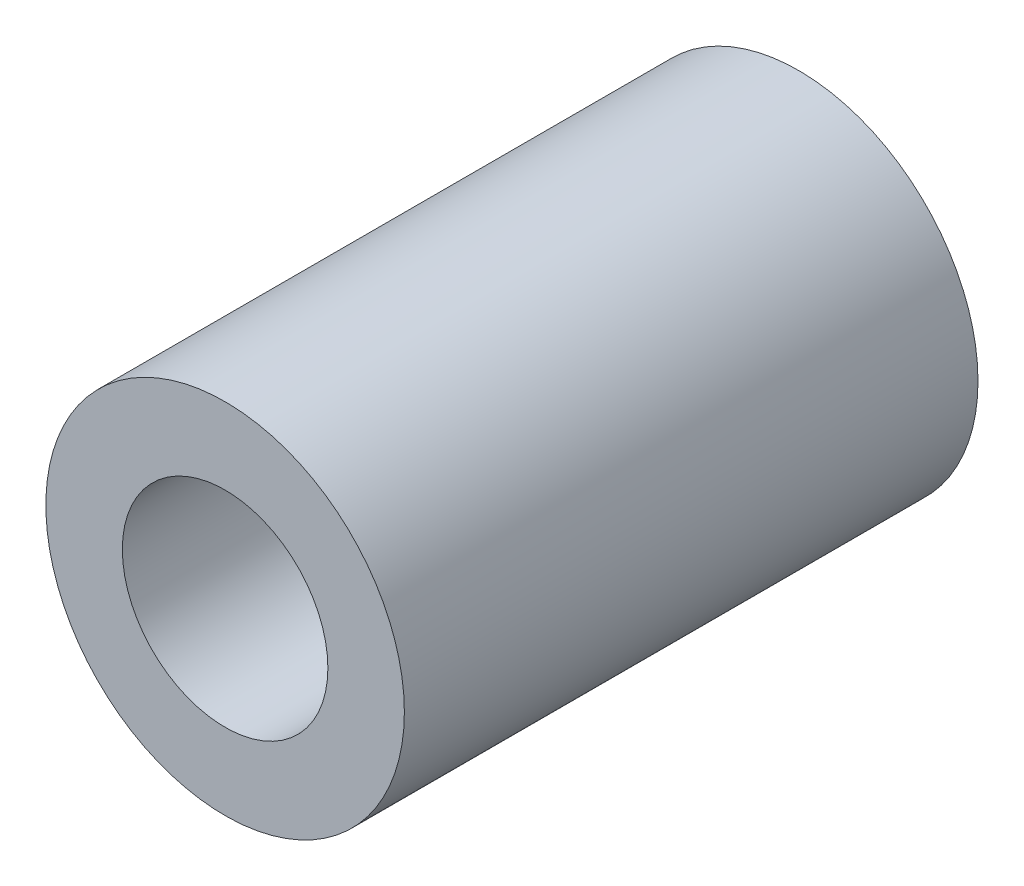
SolidWorks part; units mm, degrees
ref_plane "Alzado" through (0, 0, 0) normal (0, 0, 1) x (1, 0, 0)
ref_plane "Planta" through (0, 0, 0) normal (0, 1, 0) x (1, 0, 0)
ref_plane "Vista lateral" through (0, 0, 0) normal (1, 0, 0) x (0, 0, -1)
sketch "Croquis1" plane through (0, 0, 0) normal (0, 0, 1) x (1, 0, 0)
  circle A0 centre (0, 0) radius 7.5
  circle A1 centre (0, 0) radius 4.3
  dimension "D1" = 15
  dimension "D2" = 8.6
extrude "Saliente-Extruir1" add sketch "Croquis1" along normal blind 24
